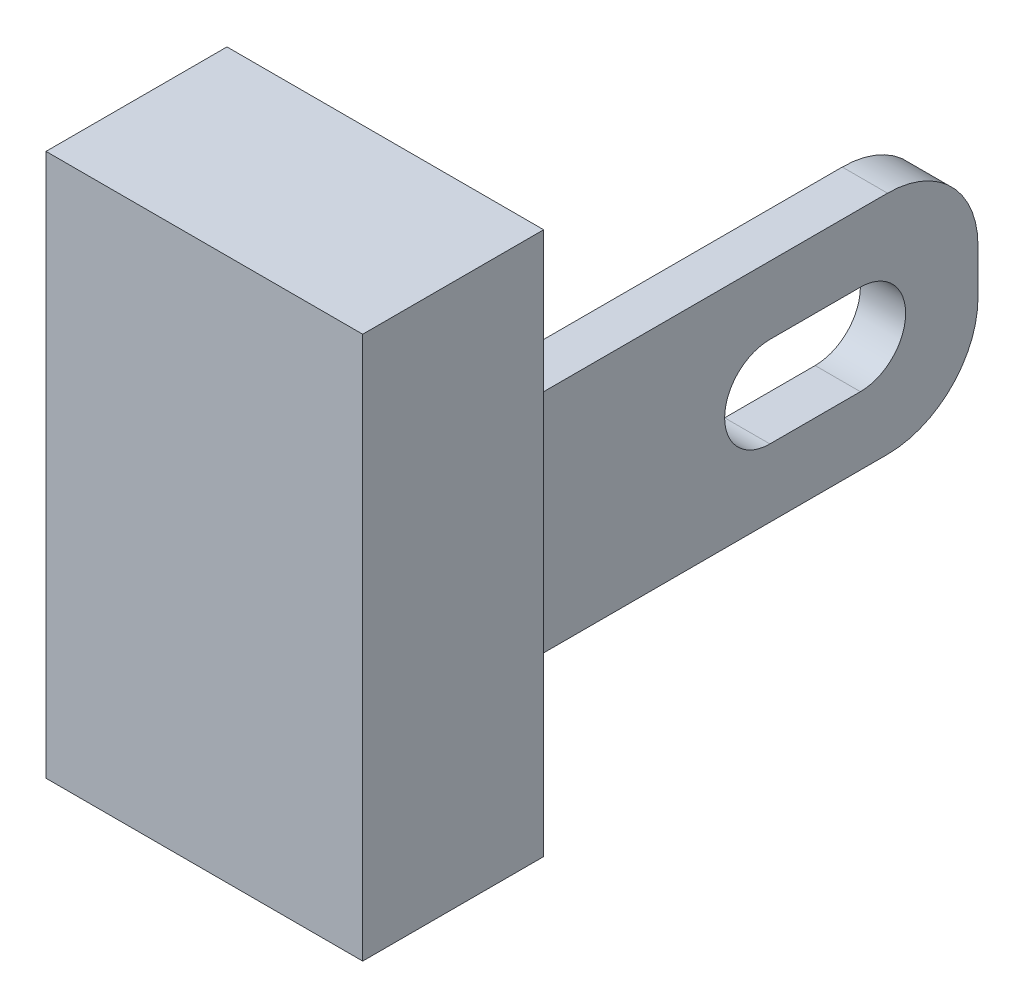
SolidWorks part; units mm, degrees
ref_plane "前视基准面" through (0, 0, 0) normal (0, 0, 1) x (1, 0, 0)
ref_plane "上视基准面" through (0, 0, 0) normal (0, 1, 0) x (1, 0, 0)
ref_plane "右视基准面" through (0, 0, 0) normal (1, 0, 0) x (0, 0, -1)
other "Configuration Table"
sketch "Sketch1" plane through (0, 0, 0) normal (0, 0, 1) x (1, 0, 0)
  line L1 (-1.75, 3) -> (1.75, 3)
  line L2 (-1.75, 3) -> (-1.75, -3)
  line L3 (-1.75, -3) -> (1.75, -3)
  line L4 (1.75, 3) -> (1.75, -3)
  line L5 (-1.75, 3) -> (1.75, -3) construction
  line L6 (-1.75, -3) -> (1.75, 3) construction
  point P1 (0, 0)
  dimension "D1" = 6
  dimension "D2" = 3.5
extrude "Boss-Extrude1" add sketch "Sketch1" along normal blind 2
sketch "Sketch2" plane through (0, 0, 0) normal (0, 0, -1) x (-1, 0, 0)
  line L0 (0, 0) -> (-1.3, 0) construction
  line L1 (-1.75, -3) -> (-1.75, 3) construction
  line L2 (-1.55, 1.25) -> (-1.05, 1.25)
  line L3 (-1.55, 1.25) -> (-1.55, -1.25)
  line L4 (-1.55, -1.25) -> (-1.05, -1.25)
  line L5 (-1.05, 1.25) -> (-1.05, -1.25)
  line L6 (-1.55, 1.25) -> (-1.05, -1.25) construction
  line L7 (-1.55, -1.25) -> (-1.05, 1.25) construction
  dimension "D1" = 0.2
  dimension "D2" = 0.5
  dimension "D3" = 2.5
extrude "Boss-Extrude2" add sketch "Sketch2" along normal blind 5
fillet "Fillet1" radius 1 2 edges at (1.3, -1.25, -5) (1.3, 1.25, -5)
sketch "Sketch3" plane through (1.55, 0, 0) normal (1, 0, 0) x (0, 0, -1)
  line L0 (2.7, 0) -> (3.7, 0) construction
  line L1 (2.7, 0.5) -> (3.7, 0.5)
  line L2 (2.7, -0.5) -> (3.7, -0.5)
  line L3 (5, 0.25) -> (5, -0.25) construction
  arc A0 (2.7, 0.5) -> (2.7, -0.5) centre (2.7, 0) ccw
  arc A1 (3.7, -0.5) -> (3.7, 0.5) centre (3.7, 0) ccw
  point P3 (3.2, 0)
  dimension "D1" = 0.5
  dimension "D2" = 1.3
  dimension "D3" = 1
extrude "Cut-Extrude1" cut sketch "Sketch3" against normal through all
